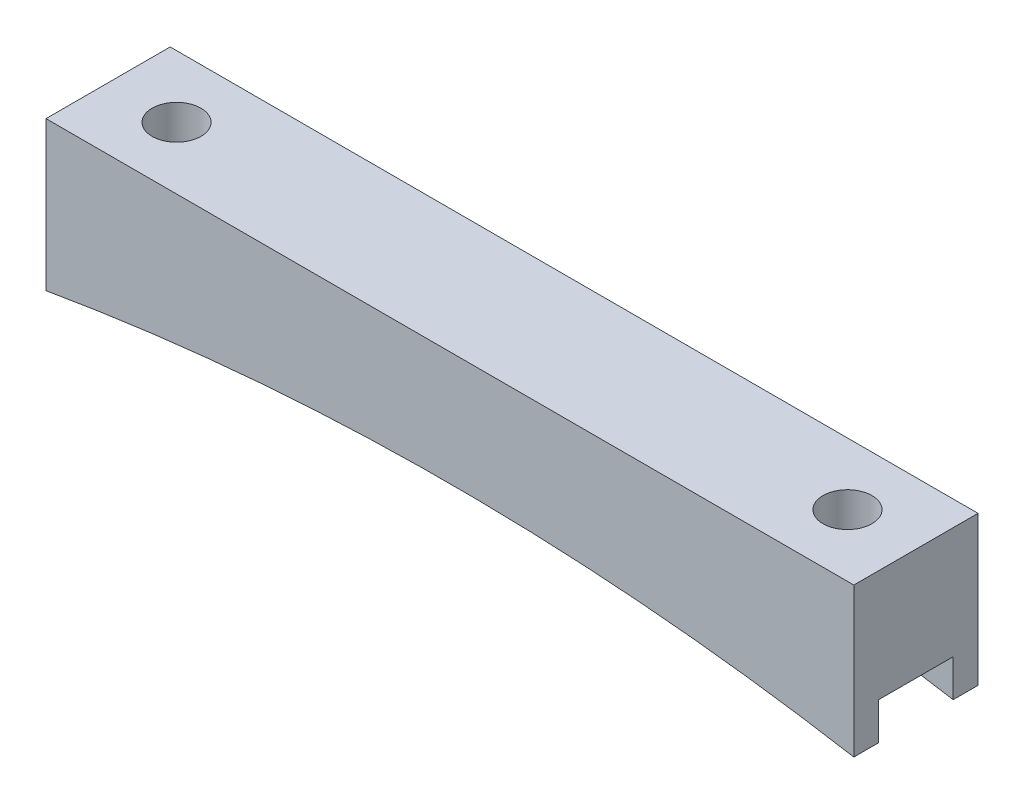
SolidWorks part; units mm, degrees
ref_plane "Front Plane" through (0, 0, 0) normal (0, 0, 1) x (1, 0, 0)
ref_plane "Top Plane" through (0, 0, 0) normal (0, 1, 0) x (1, 0, 0)
ref_plane "Right Plane" through (0, 0, 0) normal (1, 0, 0) x (0, 0, -1)
sketch "Sketch1" plane through (0, 0, 0) normal (0, 0, 1) x (1, 0, 0)
  line L0 (-41.31, 0) -> (41.31, 0)
  line L1 (-34.31, -2.54) -> (34.31, -2.54) construction
  line L2 (0, 0) -> (0, -4.6068) construction
  line L3 (41.31, 0) -> (41.31, -15.24)
  line L4 (-41.31, 0) -> (-41.31, -15.24)
  arc A0 (-41.31, -15.24) -> (41.31, -15.24) centre (0, -252.9776) cw
  point P4 (0, 0)
  point P9 (0, -2.54)
  dimension "D4" = 241.3
  dimension "D1" = 68.62
  dimension "D2" = 2.54
  dimension "D3" = 7
  dimension "D5" = 15.24
extrude "Boss-Extrude1" add sketch "Sketch1" along normal blind 12.7
sketch "Sketch2" plane through (0, 0, 0) normal (0, 1, 0) x (1, 0, 0)
  line L1 (-34.31, 0) -> (-34.31, -12.7) construction
  line L2 (-41.31, 0) -> (41.31, 0) construction
  line L3 (41.31, -12.7) -> (-41.31, -12.7) construction
  line L4 (34.31, 0) -> (34.31, -12.7) construction
  circle A0 centre (-34.31, -6.35) radius 2.5
  circle A1 centre (34.31, -6.35) radius 2.5
  circle A2 centre (-34.31, -6.35) radius 3 construction
  point P7 (-34.31, -6.35)
  dimension "D1" = 5
  dimension "D2" = 6
extrude "Cut-Extrude1" cut sketch "Sketch2" against normal through all
sketch "Sketch3" plane through (41.31, 0, 0) normal (1, 0, 0) x (0, 0, -1)
  line L0 (-12.7, -15.24) -> (0, -15.24) construction
  line L1 (-10.16, -15.24) -> (-2.54, -15.24)
  line L2 (-10.16, -15.24) -> (-10.16, -11.43)
  line L3 (-10.16, -11.43) -> (-2.54, -11.43)
  line L4 (-2.54, -15.24) -> (-2.54, -11.43)
  line L5 (-12.7, -15.24) -> (-12.7, 0) construction
  line L6 (0, -15.24) -> (0, 0) construction
  dimension "D1" = 2.54
  dimension "D2" = 2.54
  dimension "D3" = 3.81
extrude "Cut-Extrude2" cut sketch "Sketch3" against normal through all
